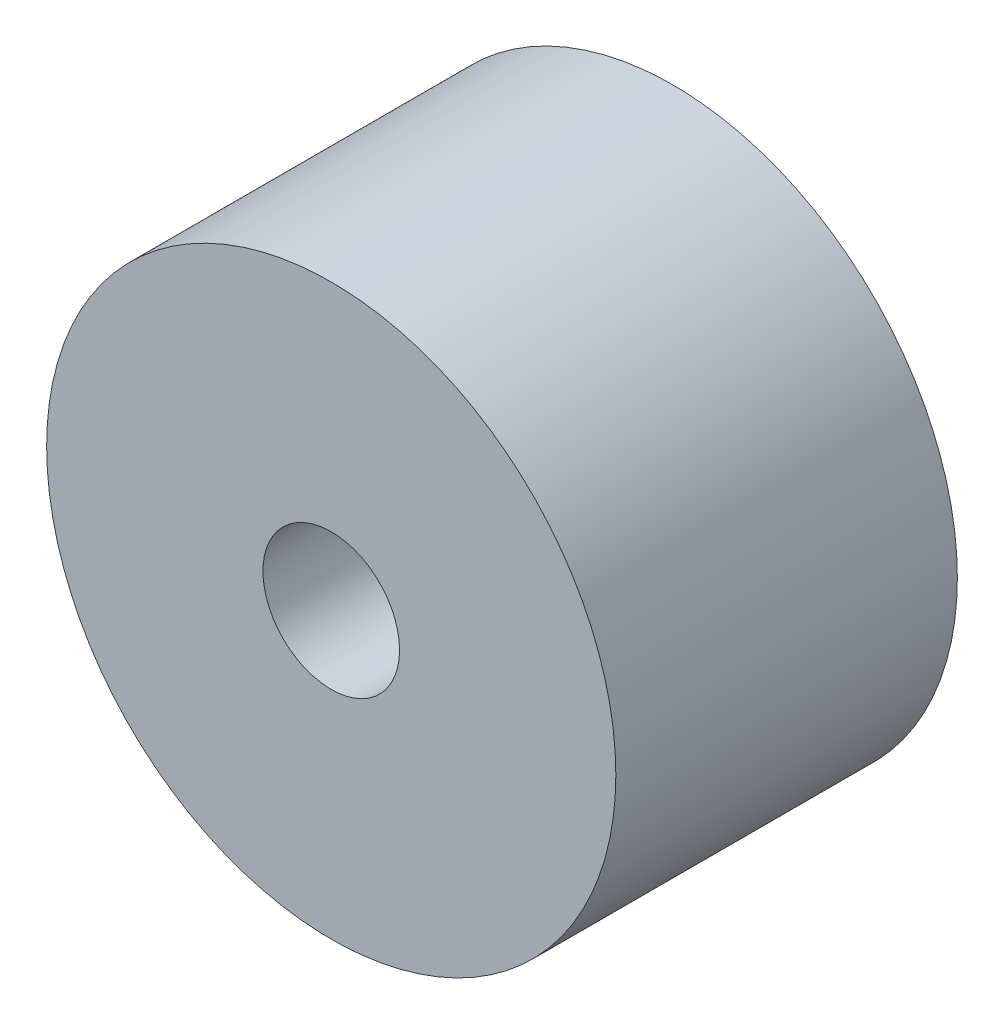
SolidWorks part; units mm, degrees
ref_plane "前视基准面" through (0, 0, 0) normal (0, 0, 1) x (1, 0, 0)
ref_plane "上视基准面" through (0, 0, 0) normal (0, 1, 0) x (1, 0, 0)
ref_plane "右视基准面" through (0, 0, 0) normal (1, 0, 0) x (0, 0, -1)
sketch "草图1" plane through (0, 0, 0) normal (0, 0, 1) x (1, 0, 0)
  circle A0 centre (0, 0) radius 25
  circle A1 centre (0, 0) radius 6
  dimension "D1" = 50
  dimension "D2" = 12
extrude "凸台-拉伸1" add sketch "草图1" along normal blind 30
